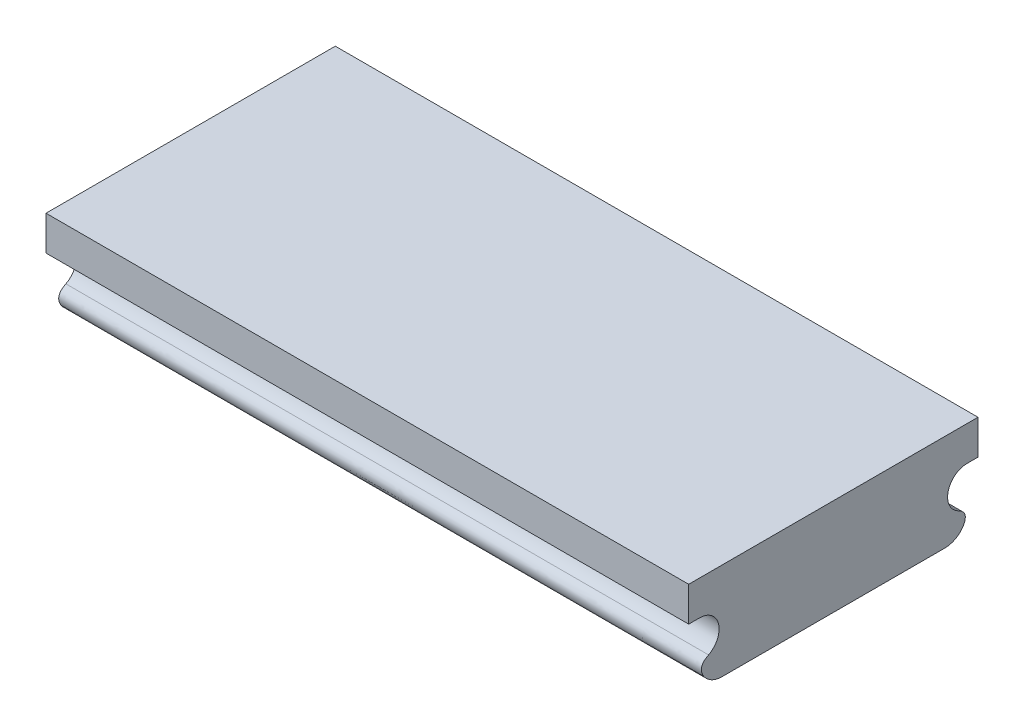
SolidWorks part; units mm, degrees
ref_plane "Front Plane" through (0, 0, 0) normal (0, 0, 1) x (1, 0, 0)
ref_plane "Top Plane" through (0, 0, 0) normal (0, 1, 0) x (1, 0, 0)
ref_plane "Right Plane" through (0, 0, 0) normal (1, 0, 0) x (0, 0, -1)
sketch "Sketch1" plane through (0, 0, 0) normal (1, 0, 0) x (0, 0, -1)
  line L0 (-23.0187, 11.9062) -> (23.0187, 11.9062) construction
  line L1 (-23.0187, 15.875) -> (23.0188, 15.875)
  line L2 (-23.0187, 15.875) -> (-23.0188, 0)
  line L3 (-23.0188, 0) -> (23.0188, 0)
  line L4 (23.0188, 15.875) -> (23.0188, 0)
  line L5 (-15.3458, 15.875) -> (-15.3458, 7.3025) construction
  line L6 (15.3458, 15.875) -> (15.3458, 7.3025) construction
  line L7 (0, 15.875) -> (0, 0) construction
  line L8 (-12.8058, 4.7625) -> (12.8058, 4.7625) construction
  line L9 (12.8058, 4.7625) -> (15.3458, 4.7625) construction
  line L10 (-16.6158, 15.875) -> (-16.6158, 11.9062)
  line L11 (-15.3458, 15.875) -> (15.3458, 15.875)
  line L12 (-16.6158, 11.9062) -> (-15.3458, 11.9062)
  line L13 (-12.8058, 4.7625) -> (12.8058, 4.7625)
  line L14 (-16.6158, 15.875) -> (-15.3458, 15.875)
  line L15 (15.3458, 15.875) -> (16.6158, 15.875)
  line L16 (16.6158, 15.875) -> (16.6158, 11.9062)
  line L17 (16.6158, 11.9062) -> (15.3458, 11.9062)
  line L18 (-23.0187, 11.9062) -> (-15.3458, 11.9062)
  line L19 (-15.3458, 10.871) -> (-15.3458, 11.9062)
  arc A0 (12.8058, 4.7625) -> (14.8932, 5.8553) centre (12.8058, 7.3025) ccw
  arc A1 (-12.8058, 4.7625) -> (-14.8932, 5.8553) centre (-12.8058, 7.3025) cw
  arc A2 (-14.3336, 7.7079) -> (-15.3458, 11.9062) centre (-15.3458, 9.685) ccw
  arc A3 (14.3336, 7.7079) -> (15.3458, 11.9062) centre (15.3458, 9.685) cw
  arc A4 (-15.3458, 11.9062) -> (-13.3282, 9.7936) centre (-15.3458, 9.8864) cw
  arc A5 (15.3458, 11.9062) -> (13.3282, 9.7936) centre (15.3458, 9.8864) ccw
  spline S0 degree 2 poles (-14.8932, 5.8553) (-15.6248, 7.0762) (-14.3336, 7.7079) knots 0 0 0 1 1 1
  spline S1 degree 2 poles (14.8932, 5.8553) (15.6248, 7.0762) (14.3336, 7.7079) knots 0 0 0 1 1 1
  spline S2 degree 3 poles (-13.4283, 4.8409) (-13.7487, 4.8973) (-14.2862, 5.1122) (-14.9247, 5.6827) (-15.3058, 6.3217) (-15.3572, 7.1633) (-14.2239, 8.1404) (-13.334, 8.7362) (-13.326, 9.8864) knots 0 0 0 0 0.146224 0.253989 0.379668 0.474368 0.603388 1 1 1 1
  spline S3 degree 3 poles (13.4283, 4.8409) (13.7487, 4.8973) (14.2862, 5.1122) (14.9247, 5.6827) (15.3058, 6.3217) (15.3572, 7.1633) (14.2239, 8.1404) (13.334, 8.7362) (13.326, 9.8864) knots 0 0 0 0 0.146224 0.253989 0.379668 0.474368 0.603388 1 1 1 1
  point P4 (0, 0)
  point P12 (23.0188, 7.9375)
  point P15 (-15.3458, 11.9062)
  point P20 (0, 11.9062)
  point P38 (16.6158, 13.8906)
  dimension "D1" = 15.875
  dimension "D2" = 46.0375
  dimension "D3" = 3.9688
  dimension "D4" = 7.6729
  dimension "D5" = 7.6729
  dimension "D6" = 4.7625
  dimension "D7" = 1.27
  dimension "D8" = 1.27
extrude "Boss-Extrude1" add sketch "Sketch1" along normal blind 73.825
equation "\"slider width\"= 1 + 13 / 16"
equation "\"slider height\"= 5 / 8"
equation "\"D1@Sketch1\"=\"slider height\""
equation "\"D2@Sketch1\"=\"slider width\""
equation "\"D3@Sketch1\"=\"slider height\"/4"
equation "\"D4@Sketch1\"=\"slider width\"/6"
equation "\"D5@Sketch1\"=\"slider width\"/6"
equation "\"D6@Sketch1\"=(\"slider height\"/4)*1.2"
